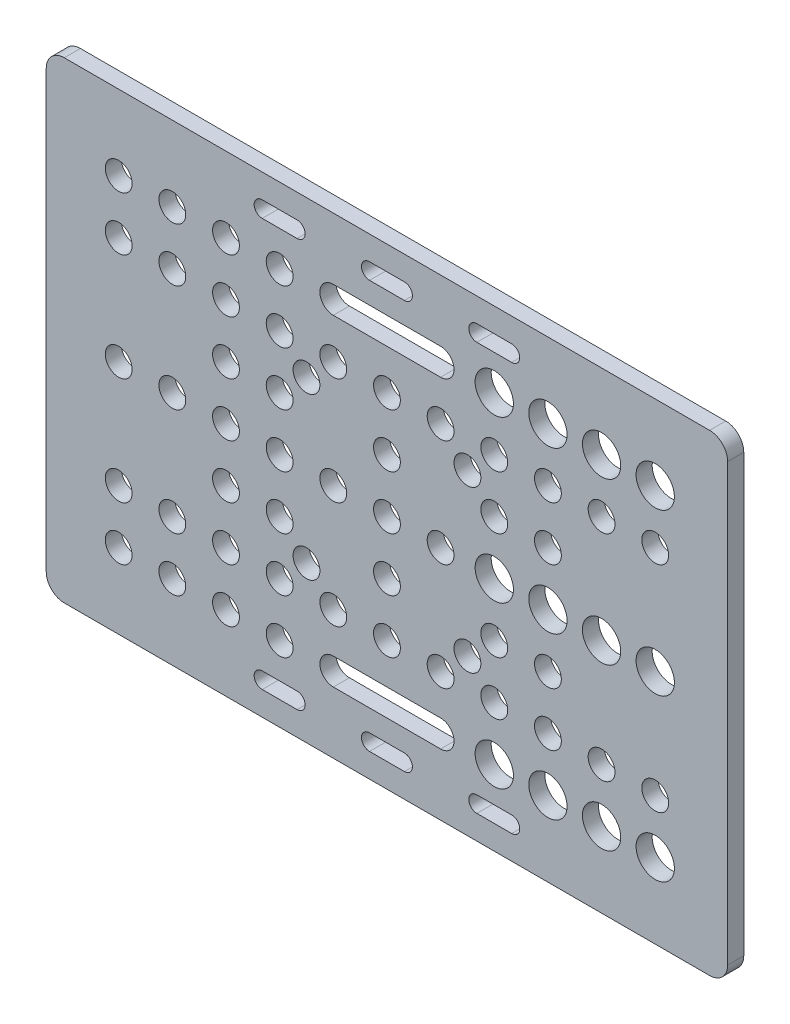
SolidWorks part; units mm, degrees
ref_plane "Front Plane" through (0, 0, 0) normal (0, 0, 1) x (1, 0, 0)
ref_plane "Top Plane" through (0, 0, 0) normal (0, 1, 0) x (1, 0, 0)
ref_plane "Right Plane" through (0, 0, 0) normal (1, 0, 0) x (0, 0, -1)
sketch "Sketch1" plane through (0, 0, 0) normal (0, 0, 1) x (1, 0, 0)
  line L0 (0, -44) -> (0, 44) construction
  line L1 (-60.14, -44) -> (60.14, -44)
  line L2 (-63.5, -40.64) -> (-63.5, 40.64)
  line L3 (-60.14, 44) -> (60.14, 44)
  line L4 (63.5, -40.64) -> (63.5, 40.64)
  line L5 (-63.5, -44) -> (63.5, 44) construction
  line L6 (-63.5, 44) -> (63.5, -44) construction
  line L7 (-10, -30) -> (10, -30) construction
  line L8 (-63.5, 0) -> (63.5, 0) construction
  line L9 (-10, -27.5) -> (10, -27.5)
  line L10 (-10, -32.5) -> (10, -32.5)
  line L11 (-23.25, -38.02) -> (-16.75, -38.02) construction
  line L12 (-23.25, -36.52) -> (-16.75, -36.52)
  line L13 (-23.25, -39.52) -> (-16.75, -39.52)
  line L14 (-20, -38.02) -> (-20, -30) construction
  line L15 (-3.25, -38.02) -> (3.25, -38.02) construction
  line L16 (-3.25, -36.52) -> (3.25, -36.52)
  line L17 (-3.25, -39.52) -> (3.25, -39.52)
  line L18 (16.75, -38.02) -> (23.25, -38.02) construction
  line L19 (16.75, -36.52) -> (23.25, -36.52)
  line L20 (16.75, -39.52) -> (23.25, -39.52)
  line L21 (-30, 0) -> (-30, -20) construction
  line L22 (-20, -10) -> (-10, -20) construction
  line L23 (-10, 30) -> (10, 30) construction
  line L24 (10, -20) -> (20, -10) construction
  line L25 (-10, 27.5) -> (10, 27.5)
  line L26 (-10, 32.5) -> (10, 32.5)
  line L27 (-23.25, 38.02) -> (-16.75, 38.02) construction
  line L28 (-23.25, 36.52) -> (-16.75, 36.52)
  line L29 (-23.25, 39.52) -> (-16.75, 39.52)
  line L30 (-3.25, 38.02) -> (3.25, 38.02) construction
  line L31 (-3.25, 36.52) -> (3.25, 36.52)
  line L32 (-3.25, 39.52) -> (3.25, 39.52)
  line L33 (16.75, 38.02) -> (23.25, 38.02) construction
  line L34 (16.75, 36.52) -> (23.25, 36.52)
  line L35 (16.75, 39.52) -> (23.25, 39.52)
  line L36 (10, 20) -> (20, 10) construction
  line L37 (-20, 10) -> (-10, 20) construction
  line L38 (-20, 38.02) -> (-20, 30) construction
  line L39 (-10, 30) -> (10, -30) construction
  line L40 (-10, -30) -> (10, 30) construction
  arc A0 (-60.14, -44) -> (-63.5, -40.64) centre (-60.14, -40.64) cw
  arc A1 (60.14, -44) -> (63.5, -40.64) centre (60.14, -40.64) ccw
  arc A2 (60.14, 44) -> (63.5, 40.64) centre (60.14, 40.64) cw
  arc A3 (-63.5, 40.64) -> (-60.14, 44) centre (-60.14, 40.64) cw
  circle A4 centre (0, -20) radius 2.5
  circle A5 centre (10, -20) radius 2.5
  circle A6 centre (20, -20) radius 2.5
  circle A7 centre (30, -20) radius 2.5
  circle A8 centre (40, -20) radius 2.5
  circle A9 centre (50, -20) radius 2.5
  circle A10 centre (-10, -20) radius 2.5
  circle A11 centre (-20, -20) radius 2.5
  circle A12 centre (-30, -20) radius 2.5
  circle A13 centre (-40, -20) radius 2.5
  circle A14 centre (-50, -20) radius 2.5
  circle A15 centre (-50, -30) radius 2.5
  circle A16 centre (-40, -30) radius 2.5
  circle A17 centre (-30, -30) radius 2.5
  circle A18 centre (-20, -30) radius 2.5
  circle A19 centre (50, -30) radius 3.57
  circle A20 centre (40, -30) radius 3.57
  circle A21 centre (30, -30) radius 3.57
  circle A22 centre (20, -30) radius 3.57
  arc A23 (-10, -27.5) -> (-10, -32.5) centre (-10, -30) ccw
  arc A24 (10, -32.5) -> (10, -27.5) centre (10, -30) ccw
  arc A25 (-23.25, -36.52) -> (-23.25, -39.52) centre (-23.25, -38.02) ccw
  arc A26 (-16.75, -39.52) -> (-16.75, -36.52) centre (-16.75, -38.02) ccw
  arc A27 (-3.25, -36.52) -> (-3.25, -39.52) centre (-3.25, -38.02) ccw
  arc A28 (3.25, -39.52) -> (3.25, -36.52) centre (3.25, -38.02) ccw
  arc A29 (16.75, -36.52) -> (16.75, -39.52) centre (16.75, -38.02) ccw
  arc A30 (23.25, -39.52) -> (23.25, -36.52) centre (23.25, -38.02) ccw
  circle A31 centre (-50, 0) radius 2.5
  circle A32 centre (-40, 0) radius 2.5
  circle A33 centre (-30, 0) radius 2.5
  circle A34 centre (-20, 0) radius 2.5
  circle A35 centre (-10, 0) radius 2.5
  circle A36 centre (0, 0) radius 2.5
  circle A37 centre (10, 0) radius 2.5
  circle A38 centre (20, 0) radius 3.57
  circle A39 centre (30, 0) radius 3.57
  circle A40 centre (40, 0) radius 3.57
  circle A41 centre (50, 0) radius 3.57
  circle A42 centre (-30, -10) radius 2.5
  circle A43 centre (-20, -10) radius 2.5
  circle A44 centre (20, -10) radius 2.5
  circle A45 centre (30, -10) radius 2.5
  circle A46 centre (0, -10) radius 2.5
  circle A47 centre (-15, -15) radius 2.5
  circle A48 centre (15, -15) radius 2.5
  arc A49 (-10, 27.5) -> (-10, 32.5) centre (-10, 30) cw
  arc A50 (10, 32.5) -> (10, 27.5) centre (10, 30) cw
  arc A51 (-23.25, 36.52) -> (-23.25, 39.52) centre (-23.25, 38.02) cw
  arc A52 (-16.75, 39.52) -> (-16.75, 36.52) centre (-16.75, 38.02) cw
  arc A53 (-3.25, 36.52) -> (-3.25, 39.52) centre (-3.25, 38.02) cw
  arc A54 (3.25, 39.52) -> (3.25, 36.52) centre (3.25, 38.02) cw
  arc A55 (16.75, 36.52) -> (16.75, 39.52) centre (16.75, 38.02) cw
  arc A56 (23.25, 39.52) -> (23.25, 36.52) centre (23.25, 38.02) cw
  circle A57 centre (15, 15) radius 2.5
  circle A58 centre (-15, 15) radius 2.5
  circle A59 centre (0, 10) radius 2.5
  circle A60 centre (30, 10) radius 2.5
  circle A61 centre (20, 10) radius 2.5
  circle A62 centre (-20, 10) radius 2.5
  circle A63 centre (-30, 10) radius 2.5
  circle A64 centre (20, 30) radius 3.57
  circle A65 centre (30, 30) radius 3.57
  circle A66 centre (40, 30) radius 3.57
  circle A67 centre (50, 30) radius 3.57
  circle A68 centre (-20, 30) radius 2.5
  circle A69 centre (-30, 30) radius 2.5
  circle A70 centre (-40, 30) radius 2.5
  circle A71 centre (-50, 30) radius 2.5
  circle A72 centre (-50, 20) radius 2.5
  circle A73 centre (-40, 20) radius 2.5
  circle A74 centre (-30, 20) radius 2.5
  circle A75 centre (-20, 20) radius 2.5
  circle A76 centre (-10, 20) radius 2.5
  circle A77 centre (50, 20) radius 2.5
  circle A78 centre (40, 20) radius 2.5
  circle A79 centre (30, 20) radius 2.5
  circle A80 centre (20, 20) radius 2.5
  circle A81 centre (10, 20) radius 2.5
  circle A82 centre (0, 20) radius 2.5
  point P0 (0, 0)
  point P61 (0, -30)
  point P68 (-20, -38.02)
  point P77 (0, -38.02)
  point P84 (20, -38.02)
  point P126 (0, 30)
  point P133 (-20, 38.02)
  point P140 (0, 38.02)
  point P147 (20, 38.02)
  dimension "D3" = 3.36
  dimension "D4" = 5
  dimension "D5" = 7.14
  dimension "D13" = 5
  dimension "D15" = 5
  dimension "D16" = 7.14
  dimension "D17" = 5
  dimension "D18" = 5
  dimension "D1" = 88
  dimension "D2" = 127
  dimension "D6" = 5
  dimension "D7" = 10
  dimension "D8" = 10
  dimension "D9" = 10
  dimension "D10" = 3
  dimension "D11" = 6.5
  dimension "D12" = 5.98
  dimension "D14" = 10
  dimension "D19" = 10
  dimension "D20" = 5
extrude "Boss-Extrude1" add sketch "Sketch1" along normal mid plane 3
